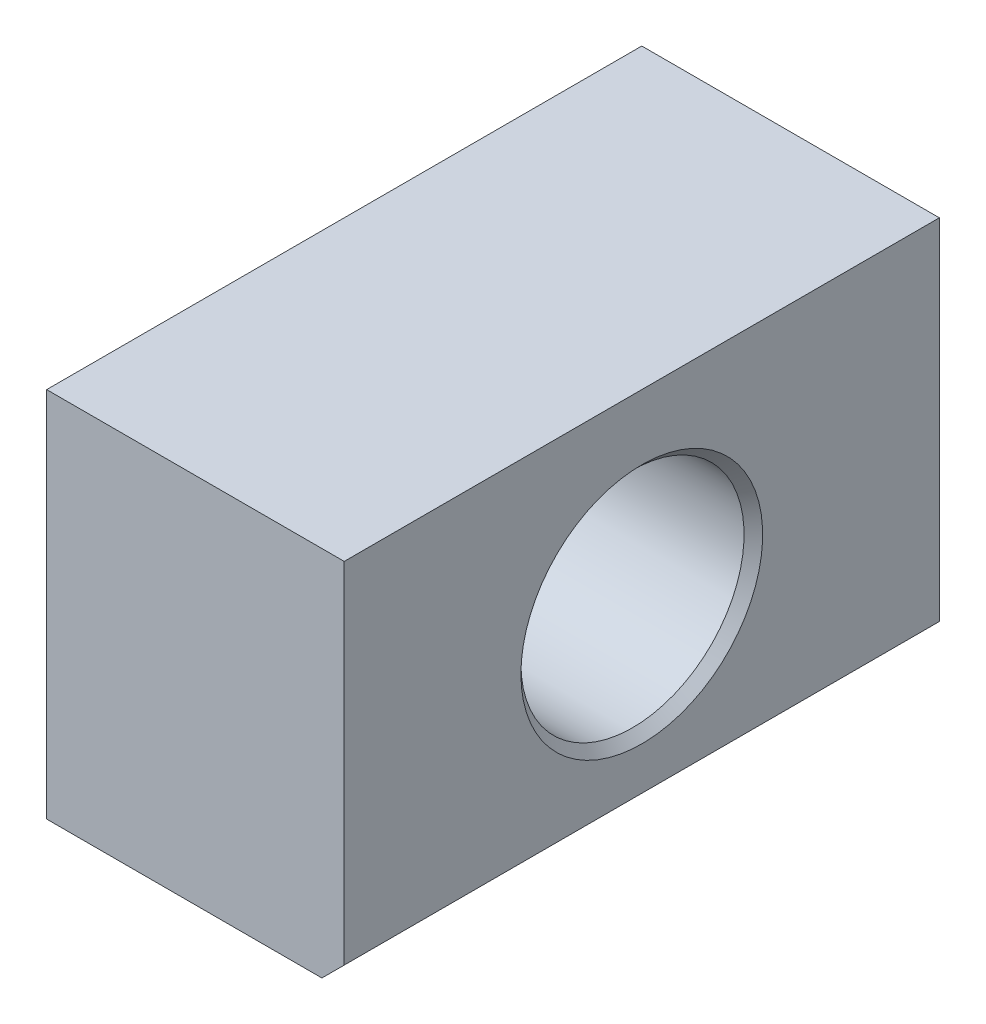
SolidWorks part; units mm, degrees
material "Простая углеродистая сталь"
ref_plane "Front" through (0, 0, 0) normal (0, 0, 1) x (1, 0, 0)
ref_plane "Top" through (0, 0, 0) normal (0, 1, 0) x (1, 0, 0)
ref_plane "Right" through (0, 0, 0) normal (1, 0, 0) x (0, 0, -1)
sketch "Эскиз1" plane through (0, 0, 0) normal (0, 0, 1) x (1, 0, 0)
  line L1 (-2, -2.5) -> (2, -2.5)
  line L2 (-2, -2.5) -> (-2, 2.5)
  line L3 (-2, 2.5) -> (2, 2.5)
  line L4 (2, -2.5) -> (2, 2.5)
  line L5 (-2, -2.5) -> (2, 2.5) construction
  line L6 (-2, 2.5) -> (2, -2.5) construction
  point P0 (0, 0)
  dimension "D1" = 4
  dimension "D2" = 5
extrude "Бобышка-Вытянуть1" add sketch "Эскиз1" along normal blind 8
hole_wizard "Отверстие обработанное метчиком M31" positions "Эскиз3" profile "Эскиз2" tap size "M3" standard "DIN" end condition through all
sketch "Эскиз3" plane through (-2, 0, 0) normal (-1, 0, 0) x (0, 0, 1)
  line L0 (0, 2.5) -> (0, -2.5) construction
  point P0 (4, 0)
  dimension "D1" = 4
sketch "Эскиз2" plane through (-2, 0, 4) normal (0, 1, 0) x (0, 0, 1)
  line L0 (0, 0) -> (0, 4)
  line L1 (0, 4) -> (1.625, 4)
  line L2 (1.5, 3.875) -> (1.5, 0.125)
  line L3 (1.5, 0.125) -> (1.625, 0)
  line L5 (1.625, 0) -> (0, 0)
  line L6 (-1.5, 0.125) -> (-1.625, 0) construction
  line L7 (1.625, 4) -> (1.5, 3.875)
  line L8 (-1.625, 4) -> (-1.5, 3.875) construction
  line L11 (0, -6.35) -> (0, 107.95) construction
  dimension "Диаметр резьбы" = 3
  dimension "Глубина проходного сверла" = 4
  dimension "Диаметр передней зенковки" = 3.25
  dimension "Угол передней зенковки" = 90
  dimension "Диаметр задней зенковки" = 3.25
  dimension "Угол задней зенковки" = 90
chamfer "Фаска1" distance 0.3 angle 45 1 edges at (2, -2.5, 4)
